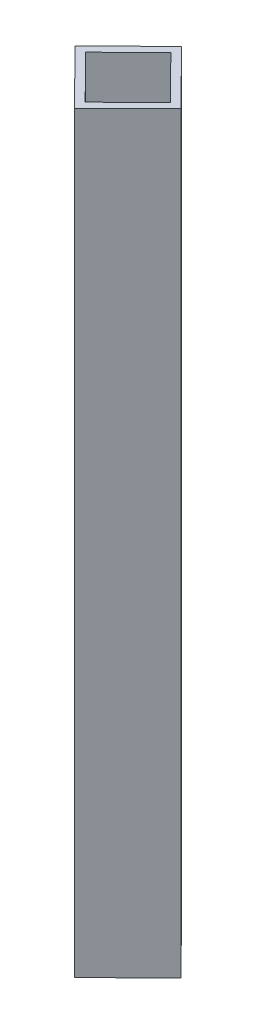
SolidWorks part; units mm, degrees
ref_plane "Front" through (0, 0, 0) normal (0, 0, 1) x (1, 0, 0)
ref_plane "Top" through (0, 0, 0) normal (0, 1, 0) x (1, 0, 0)
ref_plane "Right" through (0, 0, 0) normal (1, 0, 0) x (0, 0, -1)
sketch "Sketch1" plane through (0, 0, 0) normal (0, 1, 0) x (1, 0, 0)
  line L0 (0, 71.1833) -> (71.1771, -0.9421)
  line L1 (0, 71.1833) -> (-71.1771, 0.9421)
  line L2 (71.1771, -0.9421) -> (0, -71.1833)
  line L3 (-71.1771, 0.9421) -> (0, -71.1833)
  line L4 (0, 71.1833) -> (0, -71.1833) construction
  line L5 (71.1771, -0.9421) -> (-71.1771, 0.9421) construction
  point P1 (0, 0)
  dimension "D1" = 100
extrude "Extrude-Thin1" add sketch "Sketch1" along normal blind 1000 thin
sketch3d "3DSketch1"
  line L0 (35.5885, 900, 36.0627) -> (356.8198, 1093.7623, 157.3215) construction
  line L1 (35.5885, 1000, 36.0627) -> (35.5885, 900, 36.0627) construction
  line L2 (0, 1000, 71.1833) -> (71.1771, 1000, 0.9421) construction
  dimension "D1" = 100
